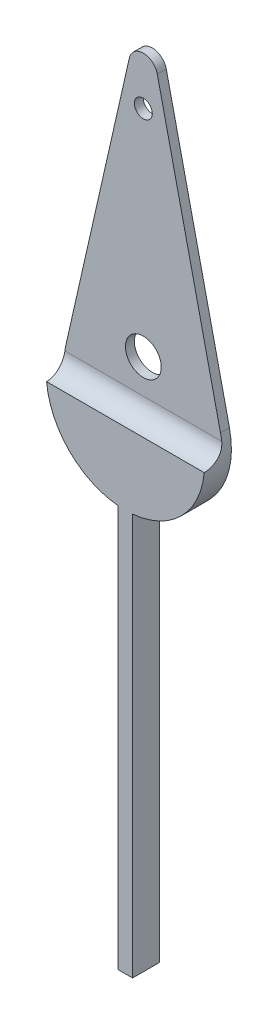
SolidWorks part; units mm, degrees
ref_plane "Front Plane" through (0, 0, 0) normal (0, 0, 1) x (1, 0, 0)
ref_plane "Top Plane" through (0, 0, 0) normal (0, 1, 0) x (1, 0, 0)
ref_plane "Right Plane" through (0, 0, 0) normal (1, 0, 0) x (0, 0, -1)
sketch "Sketch1" plane through (0, 0, 0) normal (0, 0, 1) x (1, 0, 0)
  line L0 (6, -33) -> (6, -45) construction
  line L1 (6, -27.5) -> (1.6935, -46.5252)
  line L2 (6, -27.5) -> (10.3065, -46.5252)
  line L3 (5.6, -51.8973) -> (5.6, -74.3161)
  line L4 (5.6, -45) -> (6.4, -45) construction
  line L5 (5.6, -45) -> (5.6, -51.8973) construction
  line L6 (5.6, -74.3161) -> (6.4, -74.3161)
  line L7 (6.4, -45) -> (6.4, -51.8973) construction
  line L8 (6.4, -51.8973) -> (6.4, -74.3161)
  circle A0 centre (6, -33) radius 0.5 construction
  circle A1 centre (6, -45) radius 1 construction
  circle A2 centre (6, -33) radius 0.5
  circle A3 centre (6, -45) radius 1
  arc A4 (1.6935, -46.5252) -> (5.6, -51.8973) centre (6, -47.5) ccw
  arc A5 (6.4, -51.8973) -> (10.3065, -46.5252) centre (6, -47.5) ccw
  point P11 (6, -45)
  dimension "D1" = 20
  dimension "D2" = 2.5
  dimension "D3" = 0.8
extrude "Boss-Extrude1" add sketch "Sketch1" along normal blind 1.5
sketch "Sketch2" plane through (0, 0, 0) normal (1, 0, 0) x (0, 0, -1)
  line L1 (-1.5, -14.7441) -> (-0.5, -14.7441)
  line L2 (-1.5, -14.7441) -> (-1.5, -47.8973)
  line L3 (-1.5, -47.8973) -> (-0.5, -47.8973) construction
  line L4 (-0.5, -14.7441) -> (-0.5, -46.8973)
  arc A0 (-1.5, -47.8973) -> (-0.5, -46.8973) centre (-1.5, -46.8973) ccw
  dimension "D1" = 0.5
  dimension "D2" = 4
extrude "Cut-Extrude1" cut sketch "Sketch2" against normal through all both and the other way through all
fillet "Fillet1" radius 0.8 1 edges at (6, -27.5, 0.25)
